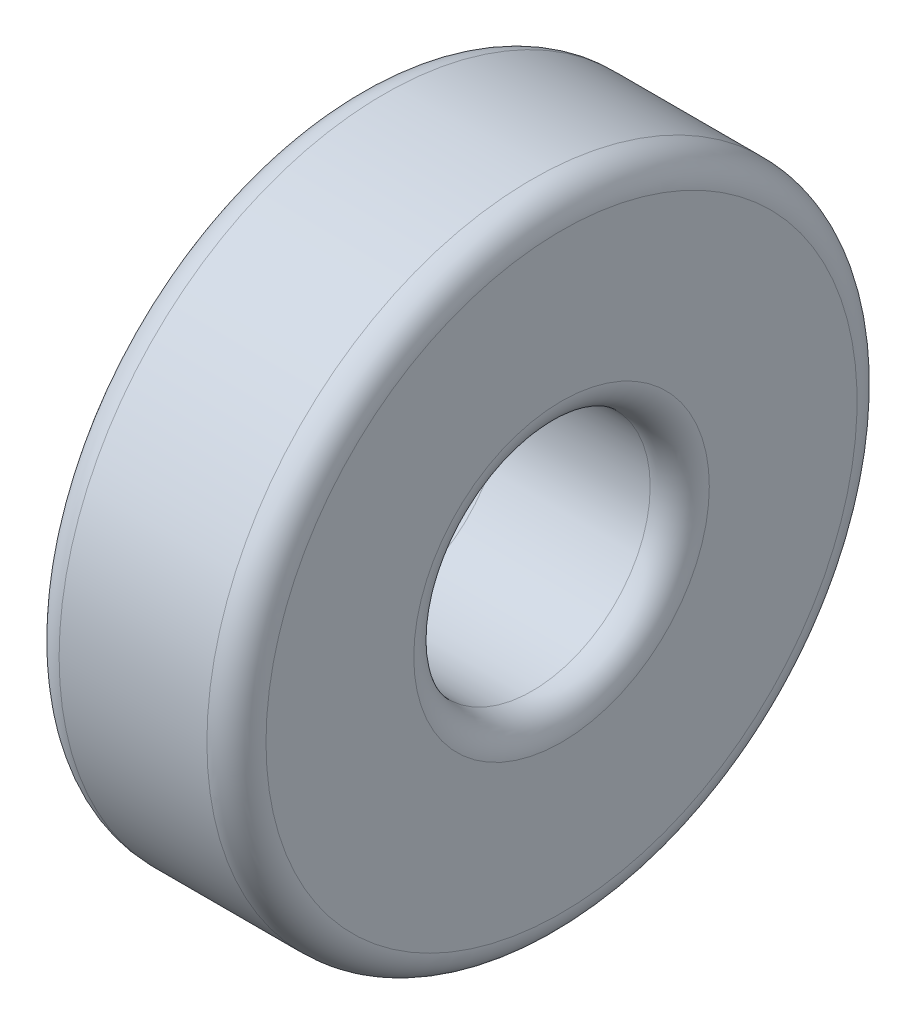
SolidWorks part; units mm, degrees
ref_plane "Front Plane" through (0, 0, 0) normal (0, 0, 1) x (1, 0, 0)
ref_plane "Top Plane" through (0, 0, 0) normal (0, 1, 0) x (1, 0, 0)
ref_plane "Right Plane" through (0, 0, 0) normal (1, 0, 0) x (0, 0, -1)
sketch "Sketch1" plane through (0, 0, 0) normal (0, 0, 1) x (1, 0, 0)
  line L0 (0, 0) -> (5504.2391, 0) construction
  line L2 (3.5, 11) -> (-3.5, 11)
  line L3 (3.5, 11) -> (3.5, 4)
  line L4 (3.5, 4) -> (-3.5, 4)
  line L5 (-3.5, 11) -> (-3.5, 4)
  line L6 (3.5, 11) -> (-3.5, 4) construction
  line L7 (3.5, 4) -> (-3.5, 11) construction
  point P3 (0, 7.5)
  dimension "D1" = 8
  dimension "D2" = 22
  dimension "D3" = 7
revolve "Revolve1" add sketch "Sketch1" angle 360 about L0
fillet "Fillet1" radius 1 4 edges at (3.5, 0, 4) (3.5, 0, 11) (-3.5, 0, 11) (-3.5, 0, 4)
